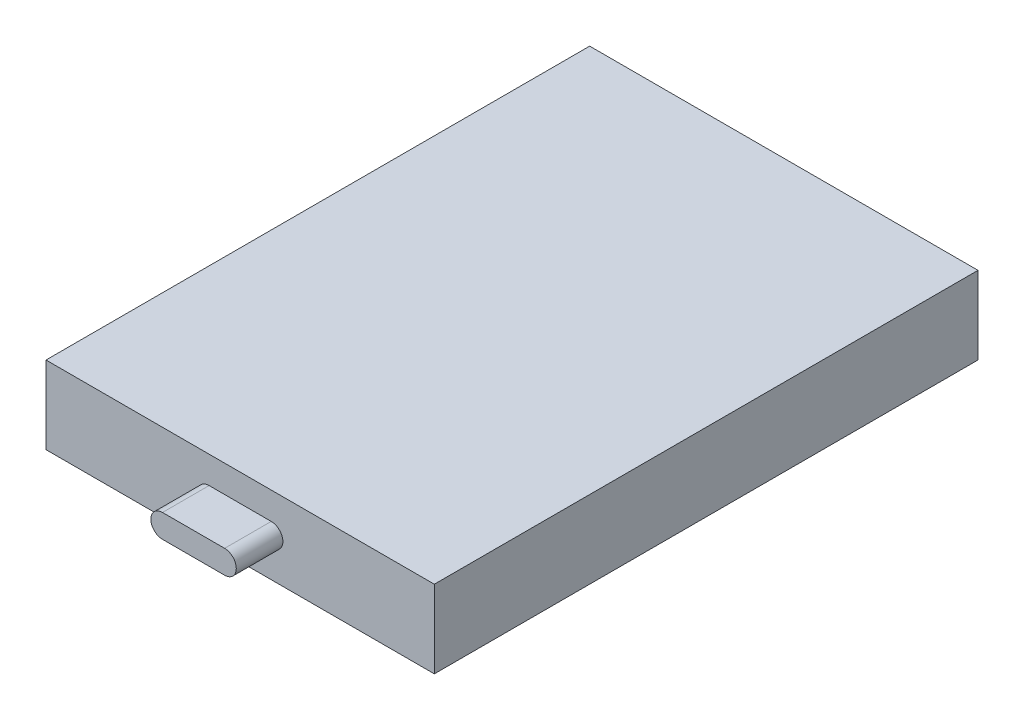
SolidWorks part; units mm, degrees
ref_plane "Front Plane" through (0, 0, 0) normal (0, 0, 1) x (1, 0, 0)
ref_plane "Top Plane" through (0, 0, 0) normal (0, 1, 0) x (1, 0, 0)
ref_plane "Right Plane" through (0, 0, 0) normal (1, 0, 0) x (0, 0, -1)
sketch "Sketch1" plane through (0, 0, 0) normal (0, 0, 1) x (1, 0, 0)
  line L1 (0, 0) -> (25, 0)
  line L2 (0, 0) -> (0, -5)
  line L3 (0, -5) -> (25, -5)
  line L4 (25, 0) -> (25, -5)
  dimension "D1" = 5
  dimension "D2" = 25
extrude "Boss-Extrude1" add sketch "Sketch1" along normal blind 35
sketch "Sketch2" plane through (0, 0, 35) normal (0, 0, 1) x (1, 0, 0)
  line L0 (0, 0) -> (25, -5) construction
  line L1 (10.5, -2.5) -> (14.5, -2.5) construction
  line L2 (10.5, -1.75) -> (14.5, -1.75)
  line L3 (10.5, -3.25) -> (14.5, -3.25)
  arc A0 (10.5, -1.75) -> (10.5, -3.25) centre (10.5, -2.5) ccw
  arc A1 (14.5, -3.25) -> (14.5, -1.75) centre (14.5, -2.5) ccw
  point P6 (12.5, -2.5)
  point P11 (12.5, -2.5)
  dimension "D1" = 1.5
  dimension "D2" = 4
extrude "Boss-Extrude2" add sketch "Sketch2" along normal blind 3
